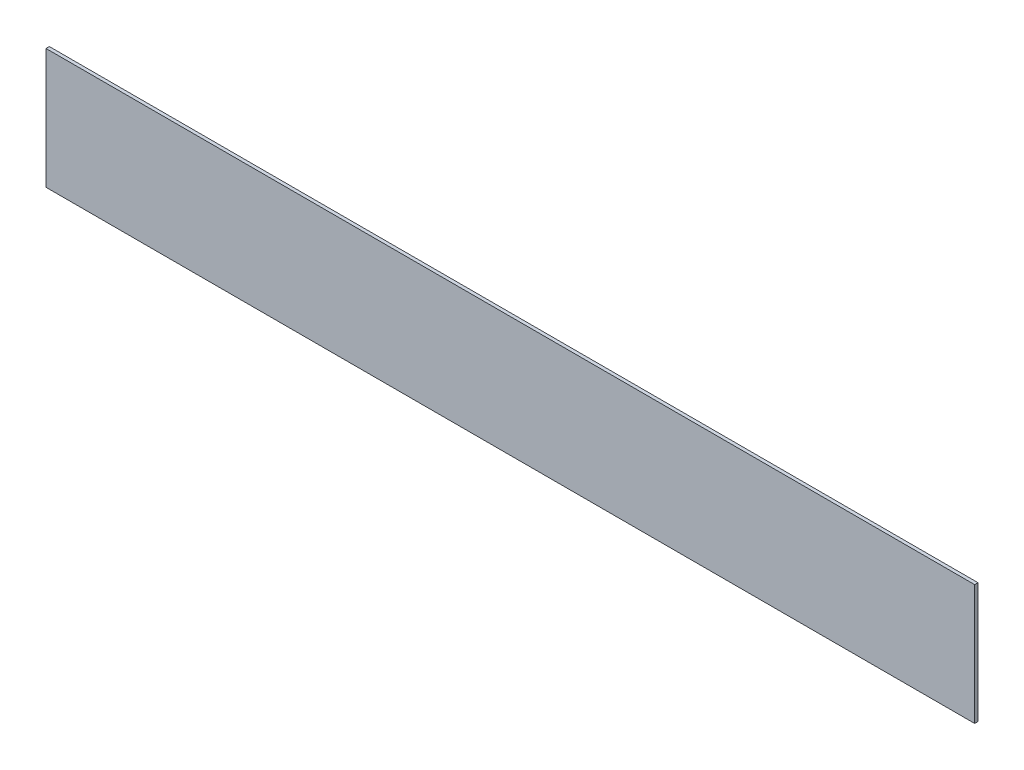
SolidWorks part; units mm, degrees
ref_plane "Front Plane" through (0, 0, 0) normal (0, 0, 1) x (1, 0, 0)
ref_plane "Top Plane" through (0, 0, 0) normal (0, 1, 0) x (1, 0, 0)
ref_plane "Right Plane" through (0, 0, 0) normal (1, 0, 0) x (0, 0, -1)
sketch "Sketch1" plane through (0, 0, 0) normal (0, 0, 1) x (1, 0, 0)
  line L1 (0, 0) -> (7061.2, 0)
  line L2 (0, 0) -> (0, -914.4)
  line L3 (0, -914.4) -> (7061.2, -914.4)
  line L4 (7061.2, 0) -> (7061.2, -914.4)
  dimension "D1" = 914.4
  dimension "D2" = 7061.2
extrude "Boss-Extrude1" add sketch "Sketch1" along normal blind 25.4
ref_plane "Plane1" through (0, 0, 25.4) normal (0, -1, 0) x (-1, 0, 0)
